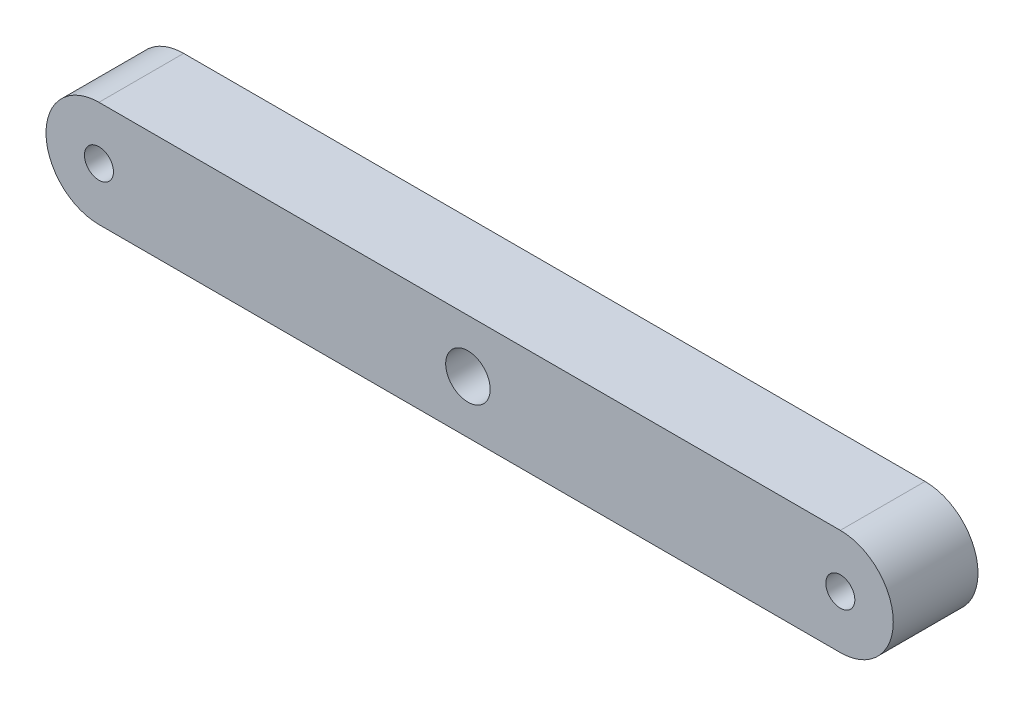
SolidWorks part; units mm, degrees
ref_plane "Front Plane" through (0, 0, 0) normal (0, 0, 1) x (1, 0, 0)
ref_plane "Top Plane" through (0, 0, 0) normal (0, 1, 0) x (1, 0, 0)
ref_plane "Right Plane" through (0, 0, 0) normal (1, 0, 0) x (0, 0, -1)
sketch "Sketch1" plane through (0, 0, 0) normal (0, 0, 1) x (1, 0, 0)
  line L0 (0, 0) -> (88.9, 0) construction
  line L1 (0, 6.35) -> (88.9, 6.35)
  line L2 (0, -6.35) -> (88.9, -6.35)
  arc A0 (0, 6.35) -> (0, -6.35) centre (0, 0) ccw
  arc A1 (88.9, -6.35) -> (88.9, 6.35) centre (88.9, 0) ccw
  point P3 (44.45, 0)
  dimension "D1" = 6.35
  dimension "D2" = 88.9
extrude "Boss-Extrude1" add sketch "Sketch1" along normal blind 10.16
sketch "Sketch2" plane through (0, 0, 10.16) normal (0, 0, 1) x (1, 0, 0)
  circle A0 centre (0, 0) radius 1.7399
  dimension "D1" = 3.4798
extrude "Cut-Extrude1" cut sketch "Sketch2" against normal through all both and the other way through all
ref_plane "Plane1" through (44.45, 0, 0) normal (1, 0, 0) x (0, 0, -1)
mirror "Mirror1" about plane through (44.45, 0, 0) normal (1, 0, 0) of "Cut-Extrude1"
sketch "Sketch3" plane through (0, 0, 10.16) normal (0, 0, 1) x (1, 0, 0)
  line L0 (88.9, 6.35) -> (0, 6.35) construction
  circle A0 centre (44.2468, 0) radius 2.667
  dimension "D1" = 5.334
  dimension "D2" = 6.35
  dimension "D3" = 44.2468
extrude "Cut-Extrude2" cut sketch "Sketch3" against normal through all both and the other way through all
